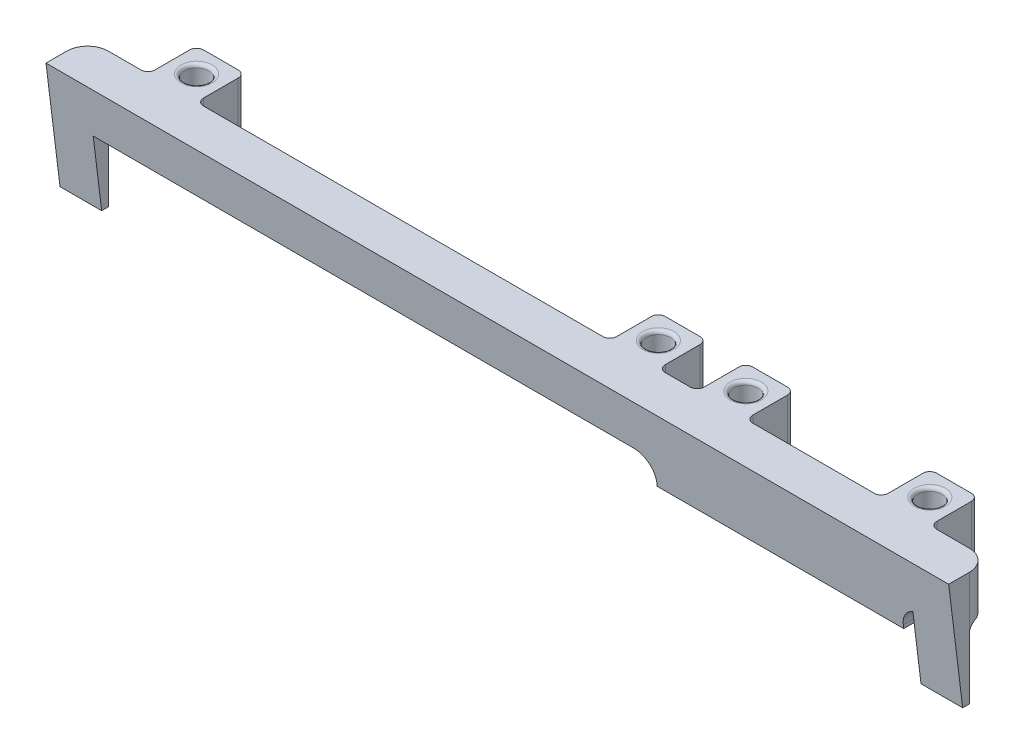
SolidWorks part; units mm, degrees
ref_plane "Front Plane" through (0, 0, 0) normal (0, 0, 1) x (1, 0, 0)
ref_plane "Top Plane" through (0, 0, 0) normal (0, 1, 0) x (1, 0, 0)
ref_plane "Right Plane" through (0, 0, 0) normal (1, 0, 0) x (0, 0, -1)
sketch "Sketch1" plane through (0, 0, 0) normal (0, 1, 0) x (1, 0, 0)
  line L0 (0, 0) -> (130, 0)
  line L1 (0, 0) -> (0, 3)
  line L2 (3, 6) -> (7.7, 6)
  line L3 (130, 3) -> (130, 0)
  line L5 (16.7, 6) -> (74.2, 6)
  line L6 (8.7, 7) -> (8.7, 12)
  line L7 (9.7, 13) -> (14.7, 13)
  line L8 (15.7, 12) -> (15.7, 7)
  line L9 (83.2, 6) -> (86.8, 6)
  line L10 (75.2, 7) -> (75.2, 12)
  line L11 (76.2, 13) -> (81.2, 13)
  line L12 (82.2, 12) -> (82.2, 7)
  line L13 (95.8, 6) -> (113.3, 6)
  line L14 (87.8, 7) -> (87.8, 12)
  line L15 (88.8, 13) -> (93.8, 13)
  line L16 (94.8, 12) -> (94.8, 7)
  line L17 (122.3, 6) -> (127, 6)
  line L18 (114.3, 7) -> (114.3, 12)
  line L19 (115.3, 13) -> (120.3, 13)
  line L20 (121.3, 12) -> (121.3, 7)
  circle A0 centre (78.7, 9.5) radius 1.75
  circle A1 centre (12.2, 9.5) radius 1.75
  circle A2 centre (91.3, 9.5) radius 1.75
  circle A3 centre (117.8, 9.5) radius 1.75
  arc A4 (127, 6) -> (130, 3) centre (127, 3) cw
  arc A5 (0, 3) -> (3, 6) centre (3, 3) cw
  arc A6 (121.3, 7) -> (122.3, 6) centre (122.3, 7) ccw
  arc A7 (120.3, 13) -> (121.3, 12) centre (120.3, 12) cw
  arc A8 (114.3, 12) -> (115.3, 13) centre (115.3, 12) cw
  arc A9 (93.8, 13) -> (94.8, 12) centre (93.8, 12) cw
  arc A10 (94.8, 7) -> (95.8, 6) centre (95.8, 7) ccw
  arc A11 (114.3, 7) -> (113.3, 6) centre (113.3, 7) cw
  arc A12 (87.8, 12) -> (88.8, 13) centre (88.8, 12) cw
  arc A13 (87.8, 7) -> (86.8, 6) centre (86.8, 7) cw
  arc A14 (82.2, 7) -> (83.2, 6) centre (83.2, 7) ccw
  arc A15 (81.2, 13) -> (82.2, 12) centre (81.2, 12) cw
  arc A16 (75.2, 12) -> (76.2, 13) centre (76.2, 12) cw
  arc A17 (75.2, 7) -> (74.2, 6) centre (74.2, 7) cw
  arc A18 (8.7, 7) -> (7.7, 6) centre (7.7, 7) cw
  arc A19 (15.7, 7) -> (16.7, 6) centre (16.7, 7) ccw
  arc A20 (14.7, 13) -> (15.7, 12) centre (14.7, 12) cw
  arc A21 (8.7, 12) -> (9.7, 13) centre (9.7, 12) cw
  point P35 (121.3, 6)
  point P44 (94.8, 6)
  point P47 (114.3, 6)
  point P52 (87.8, 6)
  point P55 (82.2, 6)
  point P62 (75.2, 6)
  point P67 (15.7, 6)
  dimension "D1" = 3
  dimension "D2" = 1
extrude "Boss-Extrude1" add sketch "Sketch1" along normal blind 6.5
sketch "Sketch3" plane through (0, 0, 0) normal (0, -1, 0) x (1, 0, 0)
  line L0 (127, -6) -> (122.3, -6)
  line L1 (121.3, -7) -> (121.3, -12)
  line L8 (120.3, -13) -> (115.3, -13)
  line L9 (114.3, -12) -> (114.3, -7)
  line L10 (94.8, -7) -> (94.8, -12)
  line L11 (93.8, -13) -> (88.8, -13)
  line L12 (87.8, -12) -> (87.8, -7)
  line L13 (122.3, -6) -> (122.3, 0)
  line L14 (0, 0) -> (130, 0) construction
  line L15 (122.3, 0) -> (86.8, 0)
  line L16 (86.8, 0) -> (86.8, -6)
  line L17 (113.3, -6) -> (95.8, -6)
  line L18 (86.8, -6) -> (3, -6)
  arc A8 (114.3, -7) -> (113.3, -6) centre (113.3, -7) ccw
  arc A9 (115.3, -13) -> (114.3, -12) centre (115.3, -12) cw
  arc A10 (121.3, -12) -> (120.3, -13) centre (120.3, -12) cw
  arc A11 (121.3, -7) -> (122.3, -6) centre (122.3, -7) cw
  arc A12 (87.8, -7) -> (86.8, -6) centre (86.8, -7) ccw
  arc A13 (88.8, -13) -> (87.8, -12) centre (88.8, -12) cw
  arc A14 (94.8, -12) -> (93.8, -13) centre (93.8, -12) cw
  arc A15 (94.8, -7) -> (95.8, -6) centre (95.8, -7) cw
  circle A16 centre (117.8, -9.5) radius 1.75
  circle A17 centre (91.3, -9.5) radius 1.75
  circle M3 centre (91.3, -9.5) radius 1.75
  arc M24 (86.8, -6) -> (87.8, -7) centre (86.8, -7) cw
  line M25 (87.8, -7) -> (87.8, -12)
  arc M26 (87.8, -12) -> (88.8, -13) centre (88.8, -12) ccw
  line M27 (88.8, -13) -> (93.8, -13)
  arc M28 (93.8, -13) -> (94.8, -12) centre (93.8, -12) ccw
  line M29 (94.8, -12) -> (94.8, -7)
  arc M30 (94.8, -7) -> (95.8, -6) centre (95.8, -7) cw
  line M31 (95.8, -6) -> (113.3, -6)
  arc M32 (113.3, -6) -> (114.3, -7) centre (113.3, -7) cw
  line M33 (114.3, -7) -> (114.3, -12)
  arc M34 (114.3, -12) -> (115.3, -13) centre (115.3, -12) ccw
  line M35 (115.3, -13) -> (120.3, -13)
  arc M36 (120.3, -13) -> (121.3, -12) centre (120.3, -12) ccw
  line M37 (121.3, -12) -> (121.3, -7)
  arc M38 (121.3, -7) -> (122.3, -6) centre (122.3, -7) cw
  line M42 (130, 0) -> (0, 0)
  circle M44 centre (117.8, -9.5) radius 1.75
extrude "Boss-Extrude2" add sketch "Sketch3" along normal blind 3.5 contours L16 L13 M42 M24 M25 M26 M27 M28 M29 M30 M31 M32 M33 M34 M35 M36 M37 M38 M3 M44
fillet "Fillet1" radius 3 2 edges at (86.8, 0, -3) (122.3, 0, -3)
fillet "Fillet2" radius 0.5 8 edges at (78.7, 6.5, -7.75) (91.3, 6.5, -7.75) (117.8, 6.5, -7.75) (12.2, 6.5, -7.75) (12.2, 0, -7.75) (78.7, 0, -7.75) (91.3, -3.5, -11.25) (117.8, -3.5, -11.25)
sketch "Sketch5" plane through (0, 0, 0) normal (-1, 0, 0) x (0, 0, 1)
  line L0 (0, 6.6153) -> (0, -3.5)
  line L1 (0, 6.6153) -> (-1.6926, -7.1697)
  line L2 (-1.6926, -7.1697) -> (0, -7.1697)
  line L3 (0, -7.1697) -> (0, -3.5)
  dimension "D1" = 7
extrude "Cut-Extrude1" cut sketch "Sketch5" against normal blind 176.5
sketch "Sketch6" plane through (0, 0, 0) normal (-1, 0, 0) x (0, 0, 1)
  line L0 (-0.8123, 0) -> (-2.0309, -9.9255)
  line L1 (-2.0309, -9.9255) -> (-3.0309, -9.9255)
  line L2 (-3.0309, -9.9255) -> (-3.0309, -3.5)
  line L3 (-1.242, -3.5) -> (-6, -3.5) construction
  line L4 (-3.0309, -3.5) -> (-3, 6.5)
  line L5 (-3, 6.5) -> (-0.0142, 6.5)
  line L6 (-0.0142, 6.5) -> (-0.8123, 0)
extrude "Boss-Extrude3" add sketch "Sketch6" against normal blind 6
fillet "Fillet3" radius 1 1 edges at (3, 0, -3.0201)
sketch "Sketch7" plane through (130, 0, 0) normal (1, 0, 0) x (0, 0, -1)
  line L0 (0.0142, 6.5) -> (2.0309, -9.9255)
  line L1 (2.0309, -9.9255) -> (3.0309, -9.9255)
  line L2 (3.0309, -9.9255) -> (3, 6.5)
  line L3 (3, 6.5) -> (0.0142, 6.5)
extrude "Boss-Extrude4" add sketch "Sketch7" against normal blind 6
fillet "Fillet4" radius 1 2 edges at (124.6333, -0.075, -3.0124) (127.65, 0, -3.0122)
